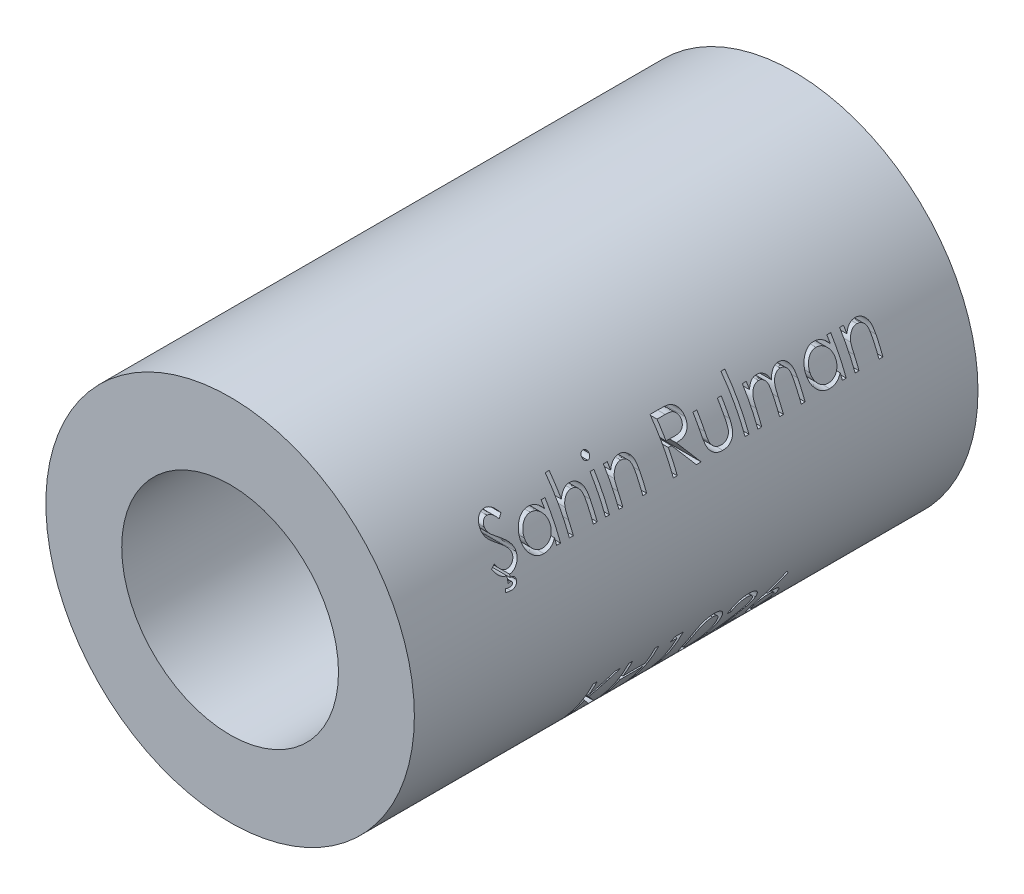
SolidWorks part; units mm, degrees
ref_plane "Front Plane" through (0, 0, 0) normal (0, 0, 1) x (1, 0, 0)
ref_plane "Top Plane" through (0, 0, 0) normal (0, 1, 0) x (1, 0, 0)
ref_plane "Right Plane" through (0, 0, 0) normal (1, 0, 0) x (0, 0, -1)
sketch "Sketch1" plane through (0, 0, 0) normal (0, 0, 1) x (1, 0, 0)
  circle A0 centre (0, 0) radius 8.5
  circle A1 centre (0, 0) radius 5
  dimension "D1" = 17
  dimension "D2" = 10
extrude "Boss-Extrude1" add sketch "Sketch1" along normal mid plane 26
ref_plane "Plane1" through (8.5, 0, 0) normal (1, 0, 0) x (0, 0, -1)
sketch "Sketch2" plane through (8.5, 0, 0) normal (1, 0, 0) x (0, 0, -1)
  text T0 "Şahin Rulman\r\n\r\n      KH1026" font "Century Gothic" height 2
extrude "Cut-Extrude1" cut sketch "Sketch2" against normal blind 3
